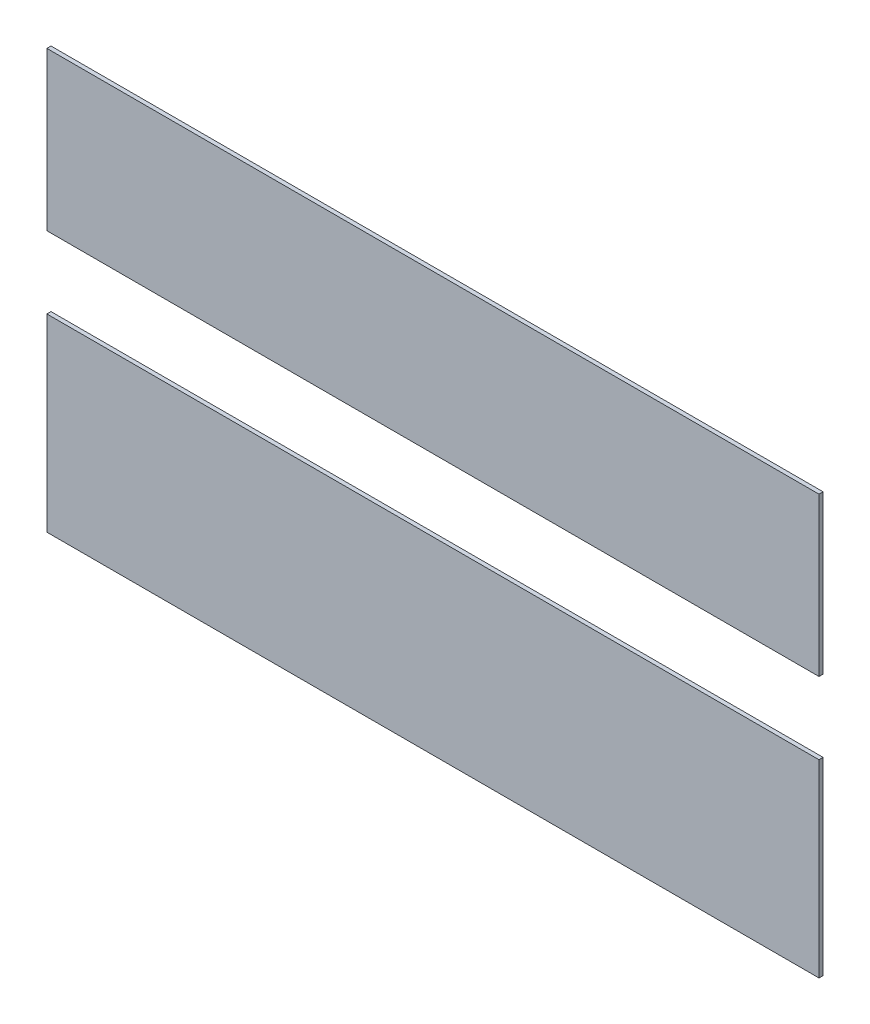
SolidWorks part; units mm, degrees
ref_plane "Front Plane" through (0, 0, 0) normal (0, 0, 1) x (1, 0, 0)
ref_plane "Top Plane" through (0, 0, 0) normal (0, 1, 0) x (1, 0, 0)
ref_plane "Right Plane" through (0, 0, 0) normal (1, 0, 0) x (0, 0, -1)
sketch "Sketch1" plane through (0, 0, 0) normal (0, 0, 1) x (1, 0, 0)
  line L0 (10323.3445, 14405.558) -> (9969.8445, 14405.558)
  line L2 (10323.3445, 14405.558) -> (10343.3423, 14405.558)
  line L4 (10343.3423, 14405.558) -> (10343.3423, 14202.0589)
  line L5 (10343.3423, 14202.0589) -> (9968.3445, 14202.0606)
  line L6 (9968.3445, 14202.0606) -> (9968.3445, 14405.558)
  line L8 (9968.3445, 14405.558) -> (9969.8445, 14405.558)
extrude "Boss-Extrude1" add sketch "Sketch1" along normal blind 2
sketch "Sketch3" plane through (0, 0, 2) normal (0, 0, 1) x (1, 0, 0)
  line L0 (9968.3445, 14405.558) -> (9968.3445, 14202.0606) construction
  line L1 (9968.3445, 14328.858) -> (10343.3423, 14328.858)
  line L6 (10343.3423, 14405.558) -> (9968.3445, 14405.558) construction
  line L13 (10343.3423, 14202.0589) -> (10343.3423, 14405.558) construction
  line L16 (9968.3445, 14293.858) -> (10343.3423, 14293.858)
  line L17 (9968.3445, 14328.858) -> (9968.3445, 14293.858)
  line L18 (10343.3423, 14328.858) -> (10343.3423, 14293.858)
  dimension "D1" = 76.7
  dimension "D2" = 111.7
extrude "Cut-Extrude2" cut sketch "Sketch3" against normal blind 10
